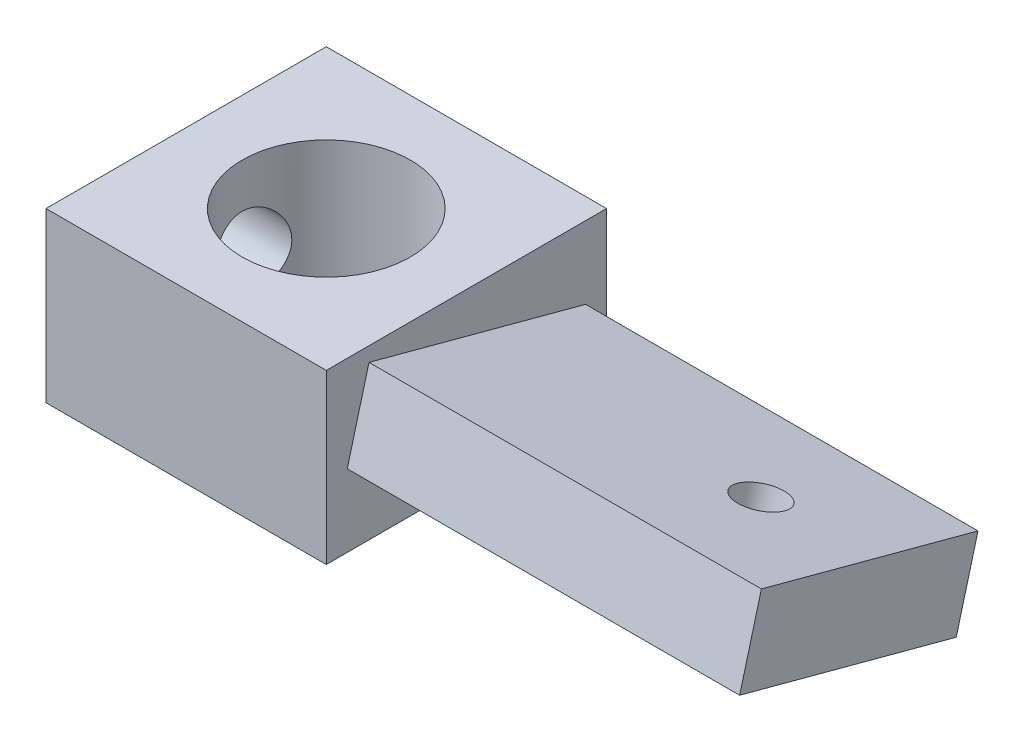
SolidWorks part; units mm, degrees
material "6061 Alloy"
ref_plane "Front Plane" through (0, 0, 0) normal (0, 0, 1) x (1, 0, 0)
ref_plane "Top Plane" through (0, 0, 0) normal (0, 1, 0) x (1, 0, 0)
ref_plane "Right Plane" through (0, 0, 0) normal (1, 0, 0) x (0, 0, -1)
sketch "Sketch1" plane through (0, 0, 0) normal (1, 0, 0) x (0, 0, -1)
  line L1 (-7.9375, 4.7625) -> (7.9375, 4.7625)
  line L2 (-7.9375, 4.7625) -> (-7.9375, -4.7625)
  line L3 (-7.9375, -4.7625) -> (7.9375, -4.7625)
  line L4 (7.9375, 4.7625) -> (7.9375, -4.7625)
  line L5 (-7.9375, 4.7625) -> (7.9375, -4.7625) construction
  line L6 (-7.9375, -4.7625) -> (7.9375, 4.7625) construction
  point P0 (0, 0)
  dimension "D1" = 9.525
  dimension "D2" = 15.875
extrude "Boss-Extrude1" add sketch "Sketch1" along normal mid plane 15.875
sketch "Sketch2" plane through (7.9375, 0, 0) normal (1, 0, 0) x (0, 0, -1)
  line L0 (-6.7499, -0.6566) -> (5.5173, -3.9436)
  line L1 (-6.7499, -0.6566) -> (-5.5173, 3.9436)
  line L2 (5.5173, -3.9436) -> (6.7499, 0.6566)
  line L3 (-5.5173, 3.9436) -> (6.7499, 0.6566)
  line L4 (-6.7499, -0.6566) -> (6.7499, 0.6566) construction
  line L5 (5.5173, -3.9436) -> (-5.5173, 3.9436) construction
  line L9 (-7.9375, -4.7625) -> (7.9375, -4.7625) construction
  point P1 (0, 0)
  dimension "D1" = 15
  dimension "D2" = 12.7
  dimension "D3" = 4.7625
extrude "Boss-Extrude2" add sketch "Sketch2" along normal blind 22.225
hole_wizard "3/8 (0.375) Diameter Hole1" positions "Sketch3" profile "Sketch4" hole size "3/8" standard "ANSI Inch" end condition through all
sketch "Sketch3" plane through (0, 4.7625, 0) normal (0, 1, 0) x (1, 0, 0)
  point P0 (0, 0)
sketch "Sketch4" plane through (0, 4.7625, 0) normal (1, 0, 0) x (0, 0, 1)
  line L0 (0, 0) -> (0, 9.525)
  line L1 (0, 9.525) -> (4.7625, 9.525)
  line L2 (4.7625, 9.525) -> (4.7625, 0)
  line L5 (4.7625, 0) -> (0, 0)
  line L11 (0, -6.35) -> (0, 107.95) construction
  dimension "Thru Hole Dia." = 9.525
  dimension "Thru Hole Depth" = 9.525
hole_wizard "#6-32 Tapped Hole1" positions "Sketch5" profile "Sketch6" tap size "#6-32" standard "ANSI Inch" end condition through all
sketch "Sketch5" plane through (0, 2.3001, -0.6163) normal (0, 0.9659, -0.2588) x (1, 0, 0)
  point P0 (24, 0)
  dimension "D1" = 24
sketch "Sketch6" plane through (24, 2.3001, -0.6163) normal (1, 0, 0) x (0, 0.2588, 0.9659)
  line L0 (0, 0) -> (0, 9.0358)
  line L1 (0, 9.0358) -> (1.3525, 9.0358)
  line L2 (1.3525, 9.0358) -> (1.3525, 0)
  line L5 (1.3525, 0) -> (0, 0)
  line L11 (0, -6.35) -> (0, 107.95) construction
  dimension "Thru Tap Drill Dia." = 2.7051
  dimension "Thru Tap Drill Depth" = 9.0358
cosmetic thread "Hole Thread1" parameters "D2"=3.5052
hole_wizard "#8 Clearance Hole1" positions "Sketch7" profile "Sketch8" hole size "#8" standard "ANSI Inch"
sketch "Sketch7" plane through (-7.9375, 0, 0) normal (1, 0, 0) x (0, 0, -1)
  point P0 (0, 0)
sketch "Sketch8" plane through (-7.9375, 0, 0) normal (0, 1, 0) x (0, 0, 1)
  line L0 (0, 0) -> (0, 20.4007)
  line L1 (0, 20.4007) -> (2.2479, 19.05)
  line L2 (2.2479, 19.05) -> (2.2479, 0)
  line L5 (2.2479, 0) -> (0, 0)
  line L10 (0, 20.4007) -> (-2.2479, 19.05) construction
  line L11 (0, -6.35) -> (0, 107.95) construction
  dimension "Hole Dia." = 4.4958
  dimension "Hole Depth" = 19.05
  dimension "Drill Angle" = 118
